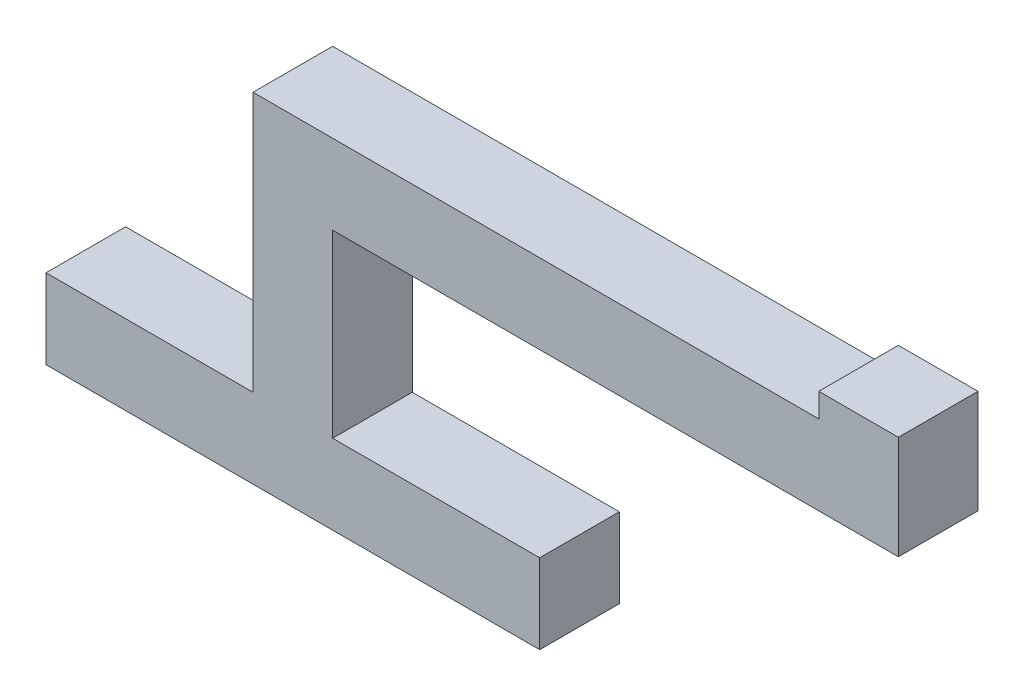
SolidWorks part; units mm, degrees
ref_plane "Front Plane" through (0, 0, 0) normal (0, 0, 1) x (1, 0, 0)
ref_plane "Top Plane" through (0, 0, 0) normal (0, 1, 0) x (1, 0, 0)
ref_plane "Right Plane" through (0, 0, 0) normal (1, 0, 0) x (0, 0, -1)
sketch "Sketch2" plane through (0, 0, 0) normal (0, 0, 1) x (1, 0, 0)
  line L2 (-63.8342, 8.1168) -> (-63.8342, -1.8832)
  line L3 (-63.8342, -1.8832) -> (-1.8342, -1.8832)
  line L6 (33.2157, 40.7475) -> (33.2157, 43.7475)
  line L7 (33.2157, 43.7475) -> (43.2157, 43.7475)
  line L8 (43.2157, 30.7475) -> (43.2157, 43.7475)
  line L12 (-1.8342, -1.8832) -> (-1.8342, 8.1168)
  line L13 (43.2157, 30.7475) -> (2.4241, 30.7475)
  line L15 (33.2157, 40.7475) -> (-37.8342, 40.7475)
  line L17 (-37.8342, 8.1168) -> (-63.8342, 8.1168)
  line L18 (-37.8342, 8.1168) -> (-37.8342, 40.7475)
  line L19 (-1.8342, 8.1168) -> (-27.8342, 8.1168)
  line L21 (2.4241, 30.7475) -> (-27.8342, 30.7475)
  line L22 (-27.8342, 8.1168) -> (-27.8342, 30.7475)
  point P15 (-27.8342, 28.4428)
  dimension "D1" = 10
  dimension "D2" = 10
  dimension "0.01" = 10
  dimension "D3" = 10
  dimension "D4" = 10
  dimension "D5" = 62
  dimension "D6" = 71.0499
  dimension "D7" = 26
  dimension "D9" = 13
extrude "Boss-Extrude1" add sketch "Sketch2" along normal blind 10
